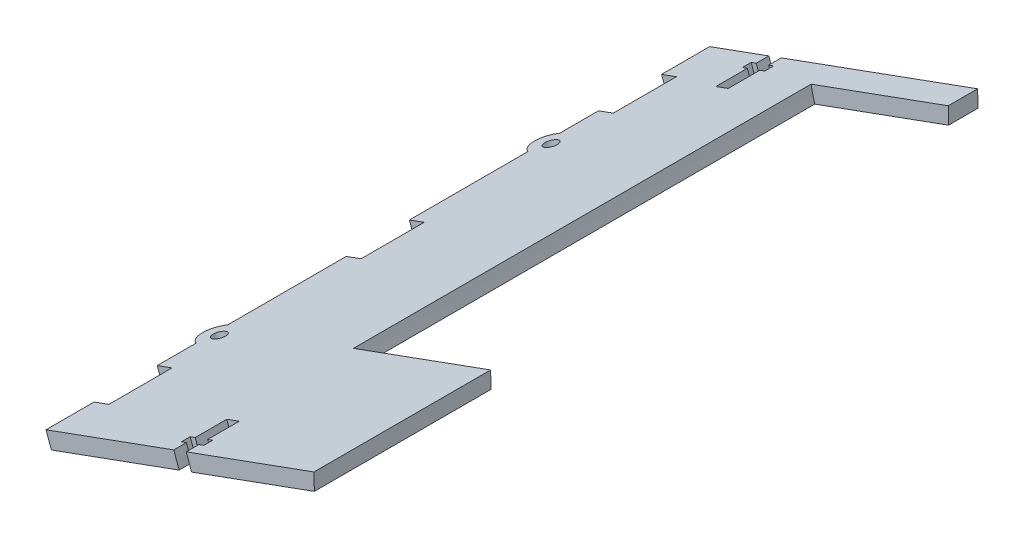
SolidWorks part; units mm, degrees
ref_plane "Front Plane" through (0, 0, 0) normal (0, 0, 1) x (1, 0, 0)
ref_plane "Top Plane" through (0, 0, 0) normal (0, 1, 0) x (1, 0, 0)
ref_plane "Right Plane" through (0, 0, 0) normal (1, 0, 0) x (0, 0, -1)
sketch "Sketch2" plane through (0, 0, 2) normal (0, 0, 1) x (1, 0, 0)
  line L1 (9867.1836, 629.0966) -> (10232.6212, 514.4475) construction
  line L3 (9824.8782, 584.8528) -> (9909.7871, 615.7306)
  line L6 (9865.6869, 624.3259) -> (10231.1244, 509.6768) construction
  line L7 (9824.8782, 584.8528) -> (9826.587, 580.1539)
  line L8 (9909.7871, 615.7306) -> (9909.9053, 610.4532)
  line L9 (9826.587, 580.1539) -> (9909.9053, 610.4532)
  line L11 (9829.5771, 586.5616) -> (9947.0505, 629.2817) construction
  line L14 (9941.3843, 264.4794) -> (9824.8782, 584.8528) construction
  circle A0 centre (9911.3826, 544.486) radius 62.5 construction
  circle A1 centre (9911.3826, 544.486) radius 67.5 construction
extrude "Boss-Extrude1" add sketch "Sketch2" along normal up to surface (210.2958 mm away)
ref_plane "Plane1" through (0, 0, 156.31) normal (0, 0, 1) x (1, 0, 0)
sketch "Sketch3" plane through (0, 0, 156.31) normal (0, 0, 1) x (1, 0, 0)
  circle A0 centre (9942.2064, 615.5926) radius 77.5
  circle A2 centre (9942.2064, 615.5926) radius 77.5 construction
extrude "Cut-Extrude1" cut sketch "Sketch3" against normal blind 145
sketch "Sketch5" plane through (959.7035, -2639.0327, 0) normal (-0.3418, 0.9398, 0) x (0.9398, 0.3418, 0)
  line L0 (9480.4479, -212.2958) -> (9476.2479, -212.2958)
  line L2 (9433.1734, -197.0589) -> (9438.1734, -197.0589)
  line L3 (9480.4479, -212.2958) -> (9480.4479, -208.2958)
  line L5 (9476.2479, -212.2958) -> (9476.2479, -208.2958)
  line L6 (9433.1734, -197.0589) -> (9433.1734, -177.0589)
  line L7 (9438.1734, -197.0589) -> (9438.1734, -177.0589)
  line L8 (9433.1734, -177.0589) -> (9438.1734, -177.0589)
  line L9 (9433.1734, -212.2958) -> (9433.1734, -2) construction
  line L10 (9482.1479, -208.2958) -> (9480.4479, -208.2958)
  line L11 (9482.1479, -208.2958) -> (9482.1479, -205.4958)
  line L12 (9438.1734, -177.0589) -> (9433.1734, -177.0589) construction
  line L13 (9433.1734, -117.1479) -> (9438.1734, -117.1479)
  line L14 (9433.1734, -117.1479) -> (9433.1734, -97.1479)
  line L15 (9438.1734, -117.1479) -> (9438.1734, -97.1479)
  line L16 (9433.1734, -97.1479) -> (9438.1734, -97.1479)
  line L17 (9438.1734, -97.1479) -> (9433.1734, -97.1479) construction
  line L18 (9433.1734, -37.237) -> (9438.1734, -37.237)
  line L19 (9433.1734, -37.237) -> (9433.1734, -17.237)
  line L20 (9438.1734, -37.237) -> (9438.1734, -17.237)
  line L21 (9433.1734, -17.237) -> (9438.1734, -17.237)
  line L22 (9433.1734, -212.2958) -> (9433.1734, -2) construction
  line L23 (9438.1734, -17.237) -> (9433.1734, -17.237) construction
  line L24 (9474.5479, -208.2958) -> (9474.5479, -205.4958)
  line L25 (9482.1479, -205.4958) -> (9480.4479, -205.4958)
  line L26 (9480.4479, -205.4958) -> (9480.4479, -195.4958)
  line L27 (9476.2479, -205.4958) -> (9476.2479, -195.4958)
  line L28 (9480.4479, -195.4958) -> (9476.2479, -195.4958)
  line L29 (9476.2479, -205.4958) -> (9474.5479, -205.4958)
  line L30 (9476.2479, -208.2958) -> (9474.5479, -208.2958)
  line L31 (9478.3479, -195.4958) -> (9478.3479, -212.2958) construction
  line L32 (9523.5224, -212.2958) -> (9433.1734, -212.2958) construction
  line L37 (9433.1734, -157.6219) -> (9433.1734, -161.8219) construction
  line L38 (9433.1734, -52.474) -> (9433.1734, -56.674) construction
  line L39 (9453.1154, -2) -> (9457.3154, -2)
  line L40 (9453.1154, -2) -> (9453.1154, -6)
  line L41 (9457.3154, -2) -> (9457.3154, -6)
  line L42 (9451.4154, -6) -> (9453.1154, -6)
  line L43 (9451.4154, -6) -> (9451.4154, -8.8)
  line L44 (9459.0154, -6) -> (9459.0154, -8.8)
  line L45 (9451.4154, -8.8) -> (9453.1154, -8.8)
  line L46 (9453.1154, -8.8) -> (9453.1154, -18.8)
  line L47 (9457.3154, -8.8) -> (9457.3154, -18.8)
  line L48 (9453.1154, -18.8) -> (9457.3154, -18.8)
  line L49 (9457.3154, -8.8) -> (9459.0154, -8.8)
  line L50 (9457.3154, -6) -> (9459.0154, -6)
  line L51 (9455.2154, -18.8) -> (9455.2154, -2) construction
  line L53 (9523.5224, -2) -> (9433.1734, -2) construction
  line L54 (9477.2575, -11.31) -> (9477.2575, -2) construction
  line L55 (9477.2575, -2) -> (9433.1734, -2) construction
  circle A4 centre (9435.6734, -159.7219) radius 2.1
  circle A5 centre (9435.6734, -54.574) radius 2.1
  point P42 (9433.1734, -54.574)
  point P48 (0, 0)
  point P52 (9433.1734, -159.7219)
  dimension "D1" = 20
  dimension "D3" = 20
  dimension "D7" = 4.2
  dimension "D8" = 4.2
  dimension "D2" = 5
  dimension "D4" = 5
  dimension "D5" = 20
  dimension "D6" = 5
  dimension "D9" = 4.2
  dimension "D10" = 1.7
  dimension "D11" = 1.7
  dimension "D12" = 2.8
  dimension "D13" = 10
  dimension "D14" = 4
  dimension "D15" = 2.5
  dimension "D16" = 2.5
  dimension "D17" = 4.2
  dimension "D18" = 1.7
  dimension "D19" = 1.7
  dimension "D20" = 2.8
  dimension "D21" = 10
  dimension "D22" = 4
extrude "Cut-Extrude2" cut sketch "Sketch5" against normal blind 5
sketch "Sketch7" plane through (959.7035, -2639.0327, 0) normal (-0.3418, 0.9398, 0) x (0.9398, 0.3418, 0)
  line L0 (9433.1734, -49.574) -> (9433.1734, -59.574)
  line L1 (9433.1734, -97.1479) -> (9433.1734, -37.237) construction
  line L2 (9433.1734, -154.7219) -> (9433.1734, -164.7219)
  line L3 (9433.1734, -177.0589) -> (9433.1734, -117.1479) construction
  arc A0 (9433.1734, -49.574) -> (9433.1734, -59.574) centre (9435.6734, -54.574) ccw
  circle A1 centre (9435.6734, -54.574) radius 2.1 construction
  arc A2 (9433.1734, -154.7219) -> (9433.1734, -164.7219) centre (9435.6734, -159.7219) ccw
  circle A3 centre (9435.6734, -159.7219) radius 2.1 construction
  dimension "D1" = 10
  dimension "D2" = 10
extrude "Boss-Extrude3" add sketch "Sketch7" against normal blind 5
